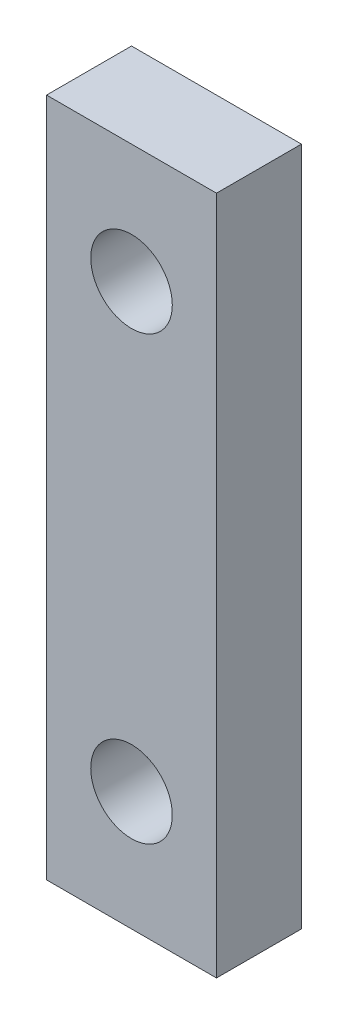
SolidWorks part; units mm, degrees
ref_plane "Front Plane" through (0, 0, 0) normal (0, 0, 1) x (1, 0, 0)
ref_plane "Top Plane" through (0, 0, 0) normal (0, 1, 0) x (1, 0, 0)
ref_plane "Right Plane" through (0, 0, 0) normal (1, 0, 0) x (0, 0, -1)
sketch "Sketch1" plane through (0, 0, 0) normal (0, 0, 1) x (1, 0, 0)
  line L1 (-5, 20) -> (5, 20)
  line L2 (-5, 20) -> (-5, -20)
  line L3 (-5, -20) -> (5, -20)
  line L4 (5, 20) -> (5, -20)
  line L5 (0, -20) -> (0, 20) construction
  line L6 (-5, 0) -> (5, 0) construction
  circle A0 centre (0, 13) radius 2.4
  circle A1 centre (0, -13) radius 2.4
  point P0 (0, 0)
  point P6 (0, 0)
  point P7 (0, 0)
  dimension "D3" = 4.8
  dimension "D1" = 40
  dimension "D2" = 10
  dimension "D4" = 13
extrude "Boss-Extrude1" add sketch "Sketch1" along normal blind 5
